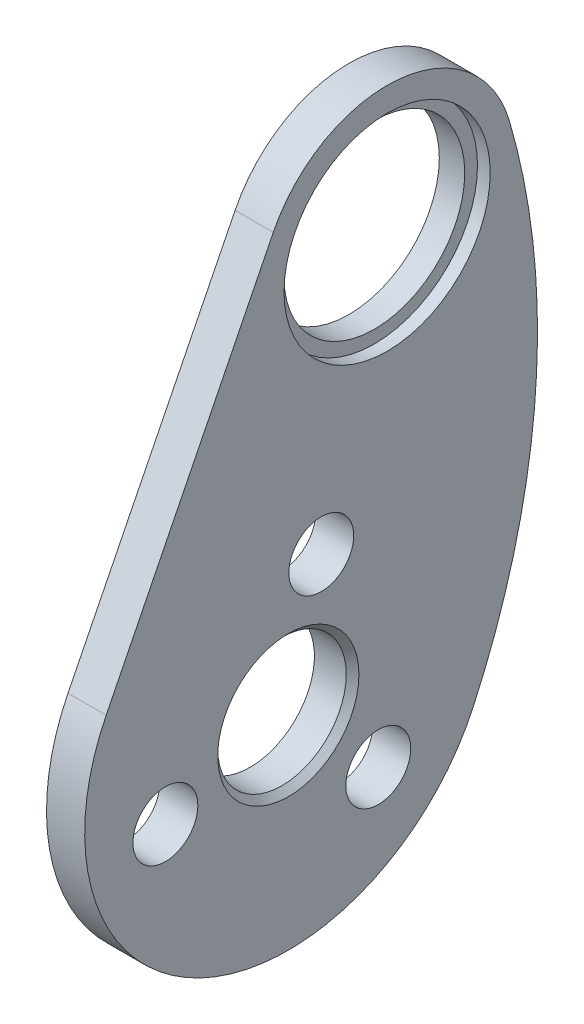
SolidWorks part; units mm, degrees
material "Thornel Mat VMA"
ref_plane "前视基准面" through (0, 0, 0) normal (0, 0, 1) x (1, 0, 0)
ref_plane "上视基准面" through (0, 0, 0) normal (0, 1, 0) x (1, 0, 0)
ref_plane "右视基准面" through (0, 0, 0) normal (1, 0, 0) x (0, 0, -1)
sketch "草图1" plane through (0, 0, 0) normal (1, 0, 0) x (0, 0, -1)
  line L0 (0, 0) -> (-7.7646, -28.9778) construction
  line L1 (-8.9465, 4.4678) -> (-22.0789, -21.8294)
  line L2 (-7.7646, -28.9778) -> (-17.2624, -28.9778) construction
  circle A0 centre (0, 0) radius 10
  circle A1 centre (-7.7646, -28.9778) radius 16
  arc A2 (6.7665, -35.6746) -> (9.5965, 2.8121) centre (-43.1841, -12.6543) ccw
  dimension "D1" = 32
  dimension "D2" = 20
  dimension "D4" = 55
  dimension "D3" = 30
  dimension "D5" = 105
extrude "凸台-拉伸1" add sketch "草图1" along normal blind 3
sketch "草图2" plane through (0, 0, 0) normal (-1, 0, 0) x (0, 0, 1)
  circle A0 centre (0, 0) radius 7.1
  arc A1 (8.9465, 4.4678) -> (-9.5965, 2.8121) centre (0, 0) ccw construction
  circle A2 centre (7.7646, -28.9778) radius 5.05
  arc A3 (-6.7665, -35.6746) -> (22.0789, -21.8294) centre (7.7646, -28.9778) ccw construction
  dimension "D1" = 14.2
  dimension "D2" = 10.1
extrude "切除-拉伸1" cut sketch "草图2" against normal blind 10
sketch "草图3" plane through (0, 0, 0) normal (-1, 0, 0) x (0, 0, 1)
  line L0 (5.1764, -19.3185) -> (7.7646, -28.9778) construction
  line L1 (7.7646, -28.9778) -> (7.7646, -5.7431) construction
  line L2 (7.7646, -28.9778) -> (-20.1149, -28.9778) construction
  circle A0 centre (5.1764, -19.3185) radius 2.55
  circle A1 centre (7.7646, -28.9778) radius 5.05 construction
  dimension "D1" = 5.1
  dimension "D2" = 10
  dimension "D3" = 15
extrude "切除-拉伸2" cut sketch "草图3" against normal blind 10
pattern_circular "阵列(圆周)1" count 3 over 360 about axis through (0, -28.9778, 7.7646) along (1, 0, 0) of "切除-拉伸2"
chamfer "倒角1" distance 0.5 angle 45 1 edges at (3, -28.9778, 2.7146)
sketch "草图4" plane through (3, 0, 0) normal (-1, 0, 0) x (0, 0, 1)
  circle A0 centre (0, 0) radius 8.1
  circle A1 centre (0, 0) radius 7.1 construction
  dimension "D1" = 16.2
extrude "切除-拉伸3" cut sketch "草图4" along normal blind 1
